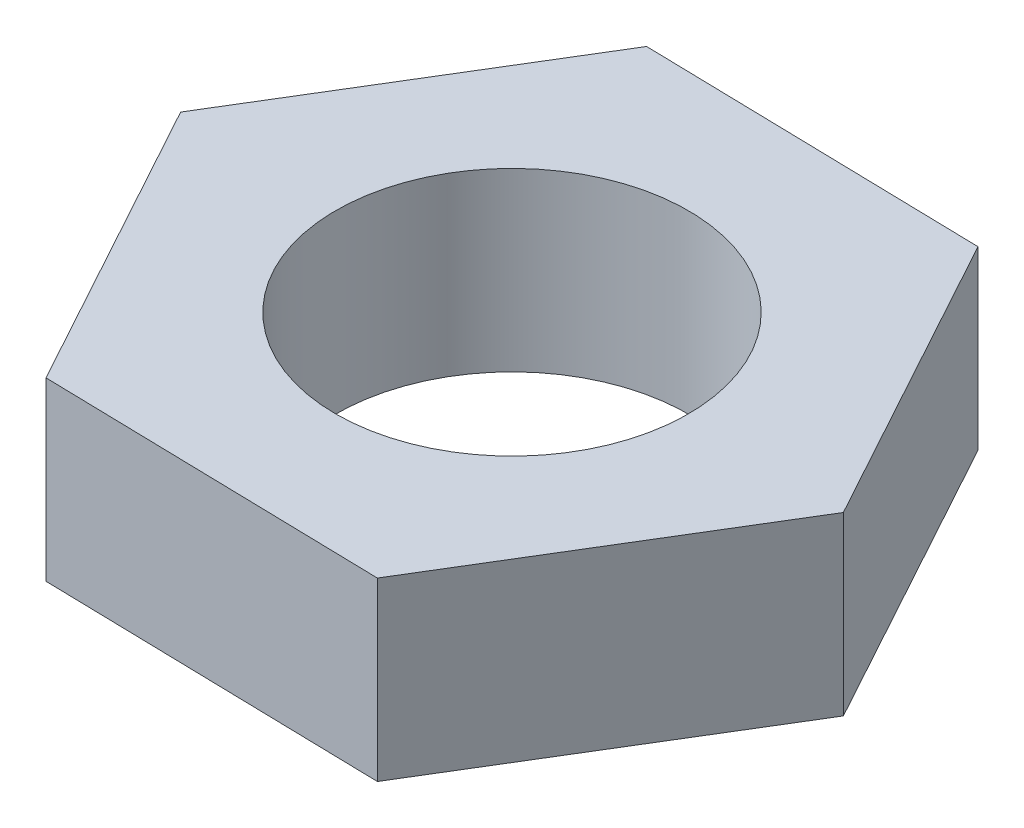
SolidWorks part; units mm, degrees
ref_plane "Plan de face" through (0, 0, 0) normal (0, 0, 1) x (1, 0, 0)
ref_plane "Plan de dessus" through (0, 0, 0) normal (0, 1, 0) x (1, 0, 0)
ref_plane "Plan de droite" through (0, 0, 0) normal (1, 0, 0) x (0, 0, -1)
sketch "Esquisse1" plane through (0, 0, 0) normal (0, 1, 0) x (1, 0, 0)
  line L1 (-19.242, 0.4376) -> (-10, -16.4452)
  line L2 (-10, -16.4452) -> (9.242, -16.8829)
  line L3 (9.242, -16.8829) -> (19.242, -0.4376)
  line L4 (19.242, -0.4376) -> (10, 16.4452)
  line L5 (10, 16.4452) -> (-9.242, 16.8829)
  line L6 (-9.242, 16.8829) -> (-19.242, 0.4376)
  circle A0 centre (0, 0) radius 16.6684 construction
extrude "Boss.-Extru.1" add sketch "Esquisse1" along normal blind 10
sketch "Esquisse2" plane through (0, 10, 0) normal (0, 1, 0) x (1, 0, 0)
  circle A0 centre (0, 0) radius 10
  dimension "D1" = 20
extrude "Enlèv. mat.-Extru.1" cut sketch "Esquisse2" against normal blind 10
